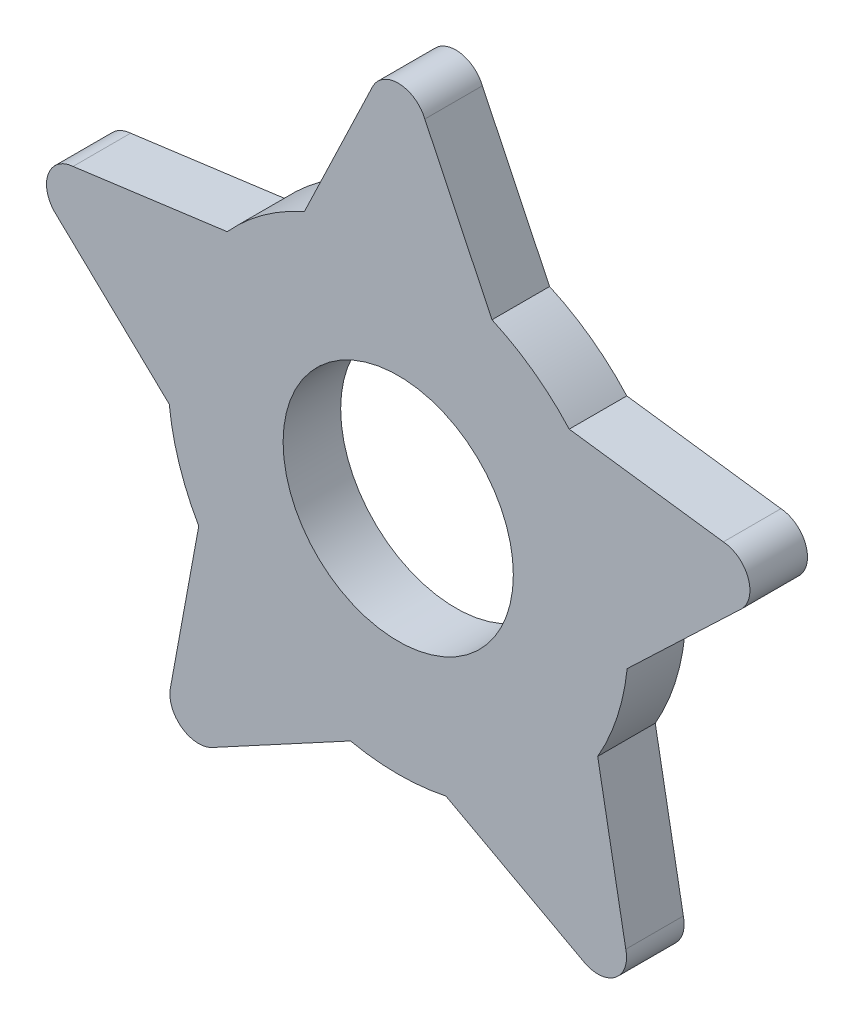
SolidWorks part; units mm, degrees
ref_plane "Front" through (0, 0, 0) normal (0, 0, 1) x (1, 0, 0)
ref_plane "Top" through (0, 0, 0) normal (0, 1, 0) x (1, 0, 0)
ref_plane "Right" through (0, 0, 0) normal (1, 0, 0) x (0, 0, -1)
sketch "Sketch1" plane through (0, 0, 0) normal (0, 0, 1) x (1, 0, 0)
  line L0 (0, 0) -> (0, 3.6531) construction
  line L1 (0, 0) -> (3.4743, 1.1289) construction
  line L2 (0, 0) -> (2.1473, -2.9555) construction
  line L3 (0, 0) -> (-2.1473, -2.9555) construction
  line L4 (0, 0) -> (-3.4743, 1.1289) construction
  line L10 (0, 3.6531) -> (0, 6.1531) construction
  line L11 (-0.4621, 5.8441) -> (0.4621, 5.8441) construction
  line L13 (-1.5, 3.6531) -> (0, 3.6531) construction
  line L14 (0, 3.6531) -> (1.5, 3.6531) construction
  line L24 (-0.4621, 6.0897) -> (-1.6293, 3.6531)
  line L25 (3.4743, 1.1289) -> (5.852, 1.9014) construction
  line L26 (2.1473, -2.9555) -> (3.6167, -4.978) construction
  line L27 (-2.1473, -2.9555) -> (-3.6167, -4.978) construction
  line L28 (-5.9344, 1.4423) -> (-3.9778, -0.4207)
  line L29 (-5.6488, 2.3213) -> (-2.9709, 2.6784)
  line L30 (-2.9709, 2.6784) -> (-3.9778, -0.4207) construction
  line L31 (-5.6488, 2.3213) -> (-5.9344, 1.4423) construction
  line L32 (-3.4743, 1.1289) -> (-6.0856, 1.9773) construction
  line L33 (0.4621, 6.0897) -> (1.6293, 3.6531)
  line L36 (5.6488, 2.3213) -> (2.9709, 2.6784)
  line L37 (5.9344, 1.4423) -> (3.9778, -0.4207)
  line L38 (3.9533, -4.655) -> (3.4654, -1.9978)
  line L39 (3.2056, -5.1983) -> (0.8291, -3.9131)
  line L40 (-3.2056, -5.1983) -> (-0.8291, -3.9131)
  line L41 (-3.9533, -4.655) -> (-3.4654, -1.9978)
  arc A0 (-1.6293, 3.6531) -> (-2.9709, 2.6784) centre (0, 0) ccw
  arc A7 (-3.9778, -0.4207) -> (-3.4654, -1.9978) centre (0, 0) ccw
  arc A8 (-0.8291, -3.9131) -> (0.8291, -3.9131) centre (0, 0) ccw
  arc A9 (3.4654, -1.9978) -> (3.9778, -0.4207) centre (0, 0) ccw
  arc A10 (2.9709, 2.6784) -> (1.6293, 3.6531) centre (0, 0) ccw
  circle A11 centre (0, 0) radius 2
  arc A12 (-5.6488, 2.3213) -> (-5.9344, 1.4423) centre (-5.61, 1.8228) ccw
  arc A15 (0.4621, 6.0897) -> (-0.4621, 6.0897) centre (0, 5.8987) ccw
  arc A16 (5.9344, 1.4423) -> (5.6488, 2.3213) centre (5.61, 1.8228) ccw
  arc A17 (3.2056, -5.1983) -> (3.9533, -4.655) centre (3.4672, -4.7722) ccw
  arc A18 (-3.9533, -4.655) -> (-3.2056, -5.1983) centre (-3.4672, -4.7722) ccw
  point P10 (0, 0)
  point P39 (0, 0)
  point P67 (0, 0)
  dimension "D1" = 8
  dimension "D3" = 5
  dimension "D9" = 4
  dimension "D4" = 0.309
  dimension "D5" = 2.5
  dimension "D6" = 3
  dimension "D7" = 1.5
  dimension "D8" = 1.6583
  dimension "D10" = 3.2586
  dimension "D11" = 0.9242
  dimension "D2" = 5
extrude "Boss-Extrude1" add sketch "Sketch1" along normal blind 1
scale "Scale1" scale about centroid uniform scaling yes scale factor 1.1
ref_plane "Plane1" through (0, 0, 0.5) normal (0, 0, 1) x (1, 0, 0)
sketch "Sketch2" plane through (0, 0, 1.05) normal (0, 0, 1) x (1, 0, 0)
  circle A0 centre (0, 0) radius 2.2 construction
  circle A1 centre (0, 0) radius 2.2
sketch "Sketch3" plane through (0, 0, 0.5) normal (0, 0, 1) x (1, 0, 0)
  circle A0 centre (0, 0) radius 2.2 construction
  circle A1 centre (0, 0) radius 2.2
